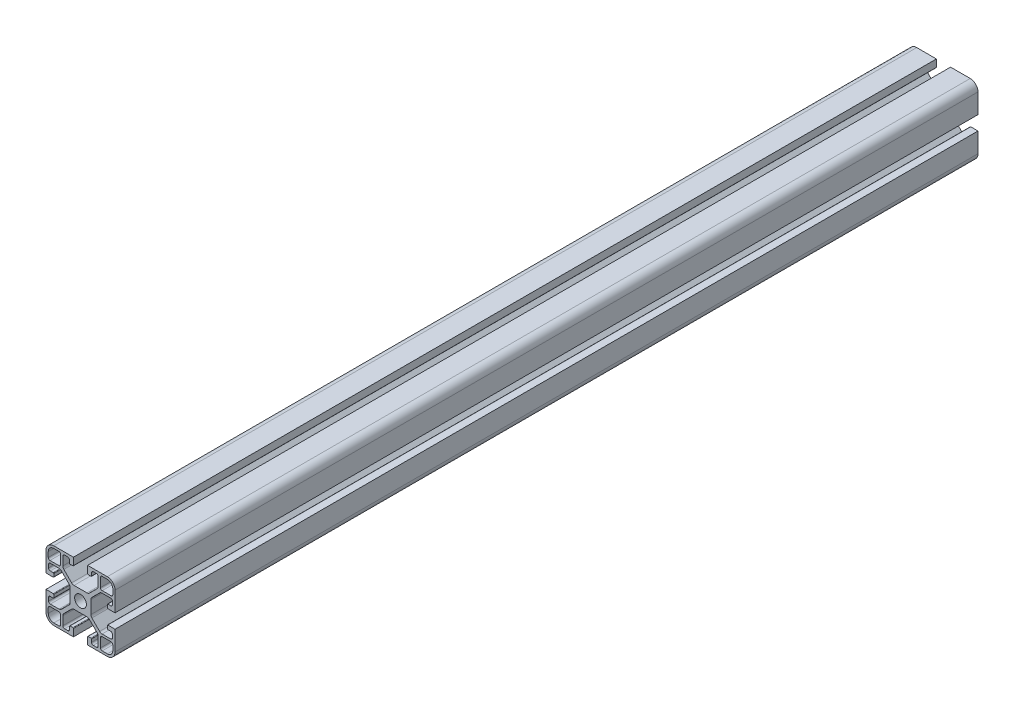
SolidWorks part; units mm, degrees
ref_plane "Front Plane" through (0, 0, 0) normal (0, 0, 1) x (1, 0, 0)
ref_plane "Top Plane" through (0, 0, 0) normal (0, 1, 0) x (1, 0, 0)
ref_plane "Right Plane" through (0, 0, 0) normal (1, 0, 0) x (0, 0, -1)
sketch "Sketch1" plane through (0, 0, 0) normal (0, 0, 1) x (1, 0, 0)
  line B0 (-20, 4.1) -> (-20, 15.5)
  arc B1 (-15.5, 20) -> (-20, 15.5) centre (-15.5, 15.5) ccw
  line B2 (-15.5, 20) -> (-4.1, 20)
  line B3 (-4.1, 20) -> (-4.1, 15.8)
  arc B4 (-4.4, 15.5) -> (-4.1, 15.8) centre (-4.4, 15.8) ccw
  line B5 (-6.1, 15.5) -> (-4.4, 15.5)
  arc B6 (-6.4, 15.8) -> (-6.1, 15.5) centre (-6.1, 15.8) ccw
  line B7 (-6.4, 17.5) -> (-6.4, 15.8)
  arc B8 (-6.4, 17.5) -> (-7.4, 18.5) centre (-7.4, 17.5) ccw
  line B9 (-7.4, 18.5) -> (-9.25, 18.5)
  arc B10 (-9.25, 18.5) -> (-10.25, 17.5) centre (-9.25, 17.5) ccw
  line B11 (-10.25, 17.5) -> (-10.25, 12.4926)
  arc B12 (-10.25, 12.4926) -> (-9.6642, 11.0784) centre (-8.25, 12.4926) ccw
  line B13 (-9.6642, 11.0784) -> (-5.1716, 6.5858)
  arc B14 (-5.1716, 6.5858) -> (-3.7574, 6) centre (-3.7574, 8) ccw
  line B15 (-3.7574, 6) -> (3.7574, 6)
  arc B16 (3.7574, 6) -> (5.1716, 6.5858) centre (3.7574, 8) ccw
  line B17 (5.1716, 6.5858) -> (9.6642, 11.0784)
  arc B18 (9.6642, 11.0784) -> (10.25, 12.4926) centre (8.25, 12.4926) ccw
  line B19 (10.25, 12.4926) -> (10.25, 17.5)
  arc B20 (10.25, 17.5) -> (9.25, 18.5) centre (9.25, 17.5) ccw
  line B21 (9.25, 18.5) -> (7.4, 18.5)
  arc B22 (7.4, 18.5) -> (6.4, 17.5) centre (7.4, 17.5) ccw
  line B23 (6.4, 15.8) -> (6.4, 17.5)
  arc B24 (6.1, 15.5) -> (6.4, 15.8) centre (6.1, 15.8) ccw
  line B25 (4.4, 15.5) -> (6.1, 15.5)
  arc B26 (4.1, 15.8) -> (4.4, 15.5) centre (4.4, 15.8) ccw
  line B27 (4.1, 15.8) -> (4.1, 20)
  line B28 (4.1, 20) -> (15.5, 20)
  arc B29 (20, 15.5) -> (15.5, 20) centre (15.5, 15.5) ccw
  line B30 (20, 15.5) -> (20, 4.1)
  line B31 (20, 4.1) -> (15.8, 4.1)
  arc B32 (15.5, 4.4) -> (15.8, 4.1) centre (15.8, 4.4) ccw
  line B33 (15.5, 6.1) -> (15.5, 4.4)
  arc B34 (15.8, 6.4) -> (15.5, 6.1) centre (15.8, 6.1) ccw
  line B35 (17.5, 6.4) -> (15.8, 6.4)
  arc B36 (17.5, 6.4) -> (18.5, 7.4) centre (17.5, 7.4) ccw
  line B37 (18.5, 7.4) -> (18.5, 9.25)
  arc B38 (18.5, 9.25) -> (17.5, 10.25) centre (17.5, 9.25) ccw
  line B39 (17.5, 10.25) -> (12.4926, 10.25)
  arc B40 (12.4926, 10.25) -> (11.0784, 9.6642) centre (12.4926, 8.25) ccw
  line B41 (11.0784, 9.6642) -> (6.5858, 5.1716)
  arc B42 (6.5858, 5.1716) -> (6, 3.7574) centre (8, 3.7574) ccw
  line B43 (6, 3.7574) -> (6, -3.7574)
  arc B44 (6, -3.7574) -> (6.5858, -5.1716) centre (8, -3.7574) ccw
  line B45 (6.5858, -5.1716) -> (11.0784, -9.6642)
  arc B46 (11.0784, -9.6642) -> (12.4926, -10.25) centre (12.4926, -8.25) ccw
  line B47 (12.4926, -10.25) -> (17.5, -10.25)
  arc B48 (17.5, -10.25) -> (18.5, -9.25) centre (17.5, -9.25) ccw
  line B49 (18.5, -9.25) -> (18.5, -7.4)
  arc B50 (18.5, -7.4) -> (17.5, -6.4) centre (17.5, -7.4) ccw
  line B51 (15.8, -6.4) -> (17.5, -6.4)
  arc B52 (15.5, -6.1) -> (15.8, -6.4) centre (15.8, -6.1) ccw
  line B53 (15.5, -4.4) -> (15.5, -6.1)
  arc B54 (15.8, -4.1) -> (15.5, -4.4) centre (15.8, -4.4) ccw
  line B55 (15.8, -4.1) -> (20, -4.1)
  line B56 (20, -4.1) -> (20, -15.5)
  arc B57 (15.5, -20) -> (20, -15.5) centre (15.5, -15.5) ccw
  line B58 (15.5, -20) -> (4.1, -20)
  line B59 (4.1, -20) -> (4.1, -15.8)
  arc B60 (4.4, -15.5) -> (4.1, -15.8) centre (4.4, -15.8) ccw
  line B61 (6.1, -15.5) -> (4.4, -15.5)
  arc B62 (6.4, -15.8) -> (6.1, -15.5) centre (6.1, -15.8) ccw
  line B63 (6.4, -17.5) -> (6.4, -15.8)
  arc B64 (6.4, -17.5) -> (7.4, -18.5) centre (7.4, -17.5) ccw
  line B65 (7.4, -18.5) -> (9.25, -18.5)
  arc B66 (9.25, -18.5) -> (10.25, -17.5) centre (9.25, -17.5) ccw
  line B67 (10.25, -17.5) -> (10.25, -12.4926)
  arc B68 (10.25, -12.4926) -> (9.6642, -11.0784) centre (8.25, -12.4926) ccw
  line B69 (9.6642, -11.0784) -> (5.1716, -6.5858)
  arc B70 (5.1716, -6.5858) -> (3.7574, -6) centre (3.7574, -8) ccw
  line B71 (3.7574, -6) -> (-3.7574, -6)
  arc B72 (-3.7574, -6) -> (-5.1716, -6.5858) centre (-3.7574, -8) ccw
  line B73 (-5.1716, -6.5858) -> (-9.6642, -11.0784)
  arc B74 (-9.6642, -11.0784) -> (-10.25, -12.4926) centre (-8.25, -12.4926) ccw
  line B75 (-10.25, -12.4926) -> (-10.25, -17.5)
  arc B76 (-10.25, -17.5) -> (-9.25, -18.5) centre (-9.25, -17.5) ccw
  line B77 (-9.25, -18.5) -> (-7.4, -18.5)
  arc B78 (-7.4, -18.5) -> (-6.4, -17.5) centre (-7.4, -17.5) ccw
  line B79 (-6.4, -15.8) -> (-6.4, -17.5)
  arc B80 (-6.1, -15.5) -> (-6.4, -15.8) centre (-6.1, -15.8) ccw
  line B81 (-4.4, -15.5) -> (-6.1, -15.5)
  arc B82 (-4.1, -15.8) -> (-4.4, -15.5) centre (-4.4, -15.8) ccw
  line B83 (-4.1, -15.8) -> (-4.1, -20)
  line B84 (-4.1, -20) -> (-15.5, -20)
  arc B85 (-20, -15.5) -> (-15.5, -20) centre (-15.5, -15.5) ccw
  line B86 (-20, -15.5) -> (-20, -4.1)
  line B87 (-20, -4.1) -> (-15.8, -4.1)
  arc B88 (-15.5, -4.4) -> (-15.8, -4.1) centre (-15.8, -4.4) ccw
  line B89 (-15.5, -6.1) -> (-15.5, -4.4)
  arc B90 (-15.8, -6.4) -> (-15.5, -6.1) centre (-15.8, -6.1) ccw
  line B91 (-17.5, -6.4) -> (-15.8, -6.4)
  arc B92 (-17.5, -6.4) -> (-18.5, -7.4) centre (-17.5, -7.4) ccw
  line B93 (-18.5, -7.4) -> (-18.5, -9.25)
  arc B94 (-18.5, -9.25) -> (-17.5, -10.25) centre (-17.5, -9.25) ccw
  line B95 (-17.5, -10.25) -> (-12.4926, -10.25)
  arc B96 (-12.4926, -10.25) -> (-11.0784, -9.6642) centre (-12.4926, -8.25) ccw
  line B97 (-11.0784, -9.6642) -> (-6.5858, -5.1716)
  arc B98 (-6.5858, -5.1716) -> (-6, -3.7574) centre (-8, -3.7574) ccw
  line B99 (-6, -3.7574) -> (-6, 3.7574)
  arc B100 (-6, 3.7574) -> (-6.5858, 5.1716) centre (-8, 3.7574) ccw
  line B101 (-6.5858, 5.1716) -> (-11.0784, 9.6642)
  arc B102 (-11.0784, 9.6642) -> (-12.4926, 10.25) centre (-12.4926, 8.25) ccw
  line B103 (-12.4926, 10.25) -> (-17.5, 10.25)
  arc B104 (-17.5, 10.25) -> (-18.5, 9.25) centre (-17.5, 9.25) ccw
  line B105 (-18.5, 9.25) -> (-18.5, 7.4)
  arc B106 (-18.5, 7.4) -> (-17.5, 6.4) centre (-17.5, 7.4) ccw
  line B107 (-15.8, 6.4) -> (-17.5, 6.4)
  arc B108 (-15.5, 6.1) -> (-15.8, 6.4) centre (-15.8, 6.1) ccw
  line B109 (-15.5, 4.4) -> (-15.5, 6.1)
  arc B110 (-15.8, 4.1) -> (-15.5, 4.4) centre (-15.8, 4.4) ccw
  line B111 (-15.8, 4.1) -> (-20, 4.1)
  line B112 (18.7, 12.55) -> (18.7, 15.5)
  arc B113 (18.7, 15.5) -> (15.5, 18.7) centre (15.5, 15.5) ccw
  line B114 (15.5, 18.7) -> (12.55, 18.7)
  arc B115 (12.55, 18.7) -> (11.55, 17.7) centre (12.55, 17.7) ccw
  line B116 (11.55, 17.7) -> (11.55, 12.55)
  arc B117 (11.55, 12.55) -> (12.55, 11.55) centre (12.55, 12.55) ccw
  line B118 (12.55, 11.55) -> (17.7, 11.55)
  arc B119 (17.7, 11.55) -> (18.7, 12.55) centre (17.7, 12.55) ccw
  line B120 (-18.7, -12.55) -> (-18.7, -15.5)
  arc B121 (-18.7, -15.5) -> (-15.5, -18.7) centre (-15.5, -15.5) ccw
  line B122 (-15.5, -18.7) -> (-12.55, -18.7)
  arc B123 (-12.55, -18.7) -> (-11.55, -17.7) centre (-12.55, -17.7) ccw
  line B124 (-11.55, -17.7) -> (-11.55, -12.55)
  arc B125 (-11.55, -12.55) -> (-12.55, -11.55) centre (-12.55, -12.55) ccw
  line B126 (-12.55, -11.55) -> (-17.7, -11.55)
  arc B127 (-17.7, -11.55) -> (-18.7, -12.55) centre (-17.7, -12.55) ccw
  circle B128 centre (0, 0) radius 3.4
  line B129 (-12.55, 18.7) -> (-15.5, 18.7)
  arc B130 (-15.5, 18.7) -> (-18.7, 15.5) centre (-15.5, 15.5) ccw
  line B131 (-18.7, 15.5) -> (-18.7, 12.55)
  arc B132 (-18.7, 12.55) -> (-17.7, 11.55) centre (-17.7, 12.55) ccw
  line B133 (-17.7, 11.55) -> (-12.55, 11.55)
  arc B134 (-12.55, 11.55) -> (-11.55, 12.55) centre (-12.55, 12.55) ccw
  line B135 (-11.55, 12.55) -> (-11.55, 17.7)
  arc B136 (-11.55, 17.7) -> (-12.55, 18.7) centre (-12.55, 17.7) ccw
  line B137 (12.55, -18.7) -> (15.5, -18.7)
  arc B138 (15.5, -18.7) -> (18.7, -15.5) centre (15.5, -15.5) ccw
  line B139 (18.7, -15.5) -> (18.7, -12.55)
  arc B140 (18.7, -12.55) -> (17.7, -11.55) centre (17.7, -12.55) ccw
  line B141 (17.7, -11.55) -> (12.55, -11.55)
  arc B142 (12.55, -11.55) -> (11.55, -12.55) centre (12.55, -12.55) ccw
  line B143 (11.55, -12.55) -> (11.55, -17.7)
  arc B144 (11.55, -17.7) -> (12.55, -18.7) centre (12.55, -17.7) ccw
sketch_block_instance "S8-4040-1"
sketch_block "S8-4040"
extrude "Boss-Extrude1" add sketch "Sketch1" along normal blind 500
